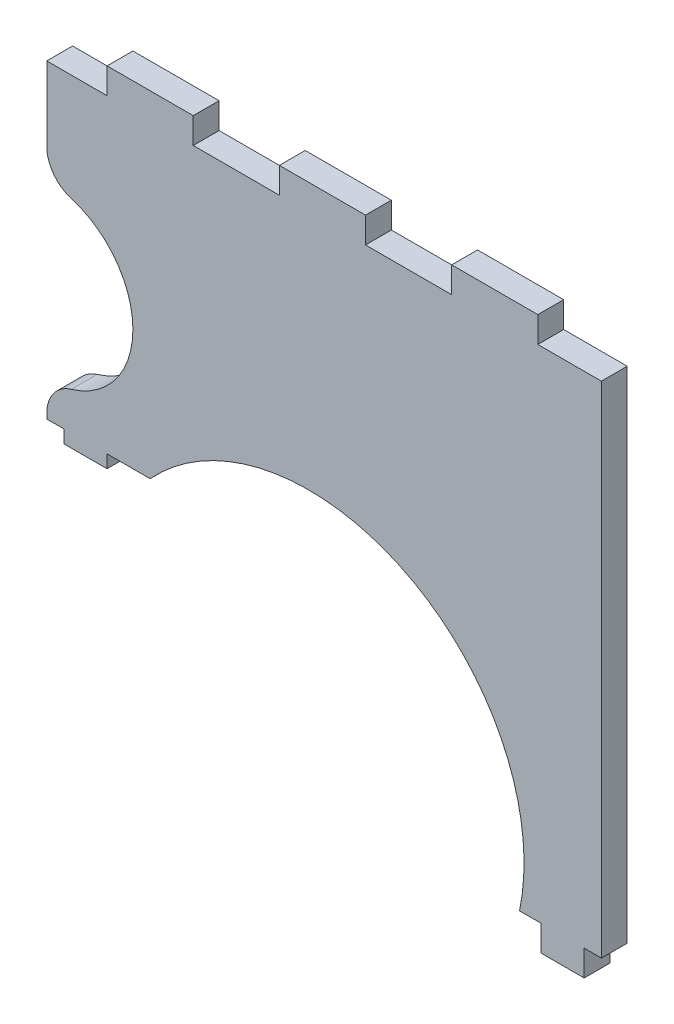
SolidWorks part; units mm, degrees
ref_plane "Alzado" through (0, 0, 0) normal (0, 0, 1) x (1, 0, 0)
ref_plane "Planta" through (0, 0, 0) normal (0, 1, 0) x (1, 0, 0)
ref_plane "Vista lateral" through (0, 0, 0) normal (1, 0, 0) x (0, 0, -1)
sketch "Croquis1" plane through (0, 0, 0) normal (0, 0, 1) x (1, 0, 0)
  line L0 (0, 0) -> (0, -3)
  line L1 (0, -3) -> (-5, -3)
  line L2 (-5, -3) -> (-5, 0)
  line L3 (-5, 0) -> (-7.5, 0)
  line L4 (0, 0) -> (2, 0)
  line L5 (2, 0) -> (2, 58)
  line L6 (2, 58) -> (-5.38, 58)
  line L7 (-5.38, 58) -> (-5.38, 61)
  line L8 (-5.38, 61) -> (-15.38, 61)
  line L9 (-15.38, 61) -> (-15.38, 58)
  line L11 (-62.38, 58) -> (-62.38, 22)
  line L12 (-62.38, 22) -> (-60.38, 22)
  line L13 (-60.38, 22) -> (-60.38, 20.5)
  line L14 (-60.38, 20.5) -> (-55.38, 20.5)
  line L15 (-55.38, 20.5) -> (-55.38, 22)
  line L16 (-55.38, 22) -> (-50.38, 22)
  line L17 (-15.38, 58) -> (-25.38, 58)
  line L18 (-25.38, 58) -> (-25.38, 61)
  line L19 (-25.38, 61) -> (-35.38, 61)
  line L20 (-35.38, 61) -> (-35.38, 58)
  line L21 (-35.38, 58) -> (-45.38, 58)
  line L22 (-45.38, 58) -> (-45.38, 61)
  line L23 (-45.38, 61) -> (-55.38, 61)
  line L24 (-55.38, 61) -> (-55.38, 58)
  line L25 (-55.38, 58) -> (-62.38, 58)
  arc A0 (-50.38, 22) -> (-7.5, 0) centre (-31.9792, 5.0763) cw
  dimension "D14" = 25
  dimension "D1" = 3
  dimension "D2" = 5
  dimension "D3" = 2.5
  dimension "D4" = 50.38
  dimension "D5" = 22
  dimension "D6" = 7
  dimension "D7" = 58
  dimension "D8" = 10
  dimension "D9" = 1.5
  dimension "D10" = 2
  dimension "D11" = 5
  dimension "D12" = 5
  dimension "D13" = 2
  dimension "D15" = 10
extrude "Saliente-Extruir1" add sketch "Croquis1" along normal blind 3
sketch "Croquis2" plane through (0, 0, 3) normal (0, 0, 1) x (1, 0, 0)
  line L0 (-62.38, 46) -> (-62.38, 26)
  line L1 (-62.38, 58) -> (-62.38, 22) construction
  line L2 (-55.38, 58) -> (-62.38, 58) construction
  arc A0 (-62.38, 46) -> (-62.38, 26) centre (-62.38, 36) cw
  point P5 (-56.8347, 36.5)
  dimension "D3" = 10
  dimension "D1" = 4
  dimension "D2" = 12
extrude "Cortar-Extruir1" cut sketch "Croquis2" against normal blind 3
fillet "Redondeo1" radius 4 2 edges at (-62.38, 46, 1.5) (-62.38, 26, 1.5)
